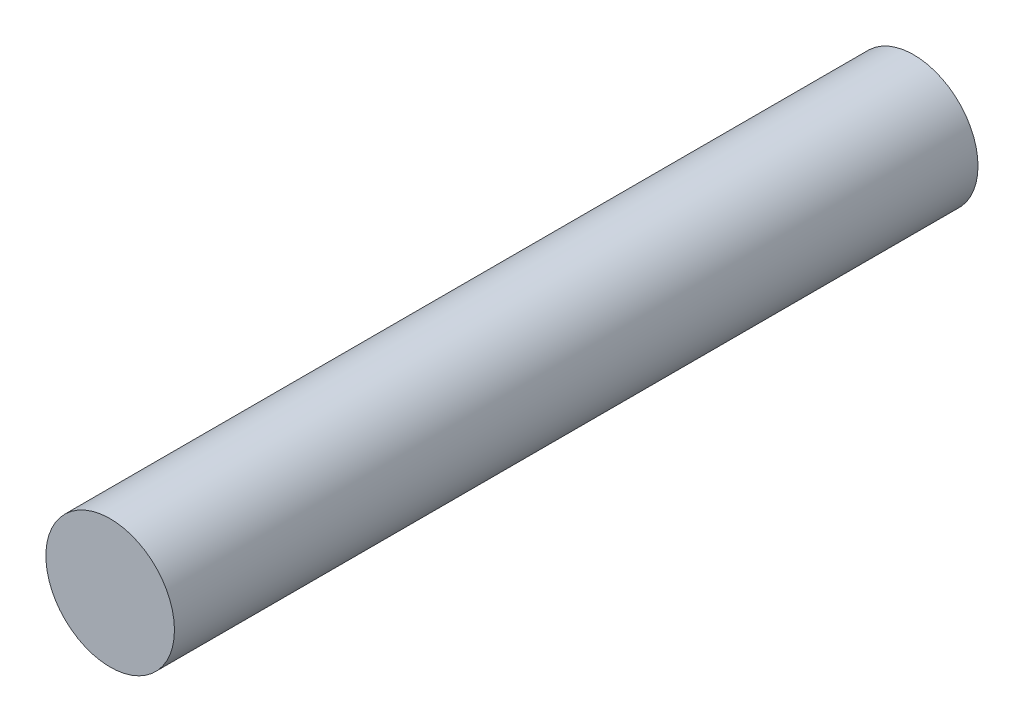
SolidWorks part; units mm, degrees
ref_plane "前视基准面" through (0, 0, 0) normal (0, 0, 1) x (1, 0, 0)
ref_plane "上视基准面" through (0, 0, 0) normal (0, 1, 0) x (1, 0, 0)
ref_plane "右视基准面" through (0, 0, 0) normal (1, 0, 0) x (0, 0, -1)
sketch "草图1" plane through (0, 0, 0) normal (0, 0, 1) x (1, 0, 0)
  circle A0 centre (0, 0) radius 4
  dimension "D1" = 8
extrude "凸台-拉伸1" add sketch "草图1" along normal blind 50
